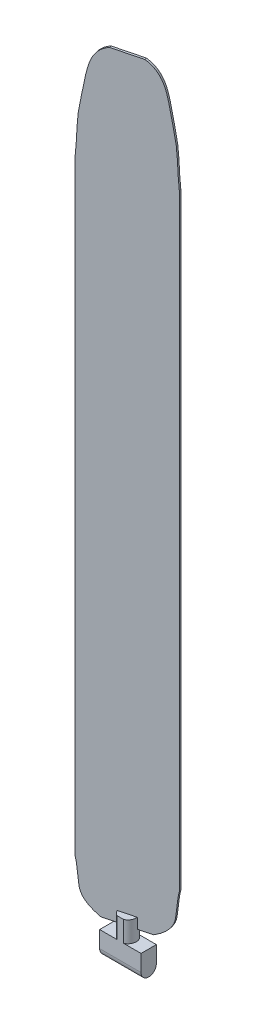
SolidWorks part; units mm, degrees
ref_plane "前视基准面" through (0, 0, 0) normal (0, 0, 1) x (1, 0, 0)
ref_plane "上视基准面" through (0, 0, 0) normal (0, 1, 0) x (1, 0, 0)
ref_plane "右视基准面" through (0, 0, 0) normal (1, 0, 0) x (0, 0, -1)
sketch "草图2" plane through (-29.3521, 0, 0) normal (1, 0, 0) x (0, 0, -1)
  line L1 (-34.5848, 63.5175) -> (-34.5848, 71.5175)
  line L2 (-34.5848, 71.5175) -> (-27.1848, 71.5175)
  line L3 (-27.1848, 71.5175) -> (-27.1848, 63.5175)
  arc A0 (-34.5848, 63.5175) -> (-27.1848, 63.5175) centre (-30.8848, 63.5175) ccw
  dimension "D1" = 8
extrude "凸台-拉伸1" add sketch "草图2" along normal mid plane 20
sketch "草图3" plane through (-29.3521, 0, 0) normal (1, 0, 0) x (0, 0, -1)
  line L0 (-34.5848, 67.3112) -> (-34.5848, -30.2762)
  line L1 (-34.5848, 18.5175) -> (-2.454, 18.5175)
sketch "草图4" plane through (0, 71.5175, 0) normal (0, 1, 0) x (1, 0, 0)
  line L0 (-39.3521, -34.5848) -> (-19.3521, -27.1848)
  line L4 (-39.3521, -27.1848) -> (-39.3521, -34.5848)
  line L5 (-39.3521, -34.5848) -> (-19.3521, -34.5848)
  line L6 (-19.3521, -34.5848) -> (-19.3521, -27.1848)
  line L7 (-19.3521, -27.1848) -> (-39.3521, -27.1848)
  line L8 (-39.3521, -27.1848) -> (-39.3521, -34.5848)
  line L9 (-39.3521, -34.5848) -> (-19.3521, -34.5848)
  line L10 (-19.3521, -34.5848) -> (-19.3521, -27.1848)
  line L11 (-19.3521, -27.1848) -> (-39.3521, -27.1848)
  circle A0 centre (-29.3521, -30.8848) radius 4
  dimension "D2" = 8
  dimension "D1" = 0
extrude "凸台-拉伸2" add sketch "草图4" along normal blind 10 contours L9 A0 L0 | L0 A0 L11
sketch "草图7" plane through (0, 81.5175, 0) normal (0, 1, 0) x (1, 0, 0)
  line L0 (-49.2279, -36.4994) -> (-49.4764, -35.5308)
  line L1 (-49.4764, -35.5308) -> (-9.4764, -25.2702)
  line L2 (-9.4764, -25.2702) -> (-9.2279, -26.2388)
  line L3 (-9.2279, -26.2388) -> (-49.2279, -36.4994)
extrude "凸台-拉伸3" add sketch "草图7" along normal blind 360 and the other way blind 5
sketch "草图8" plane through (5.7454, 0, 22.3979) normal (0.2485, 0, 0.9686) x (0.9686, 0, -0.2485)
  line L0 (-56.7531, 76.5175) -> (-40.0742, 76.5175) construction
  line L1 (-56.7531, 76.5175) -> (-56.7531, 441.5175) construction
  line L2 (-56.7531, 441.5175) -> (-15.4581, 441.5175) construction
  line L3 (-36.1056, 441.5175) -> (-36.1056, 74.8978)
  line L4 (-46.6104, 76.5175) -> (-56.7531, 76.5175)
  line L5 (-56.7531, 76.5175) -> (-56.7531, 98.1797)
  line L6 (-15.4581, 98.1797) -> (-9.3936, 70.7026)
  line L7 (-9.3936, 70.7026) -> (-25.6008, 76.5175)
  line L8 (-43.0788, 441.5175) -> (-63.9555, 450.3371)
  line L9 (-63.9555, 450.3371) -> (-56.7531, 391.6929)
  line L10 (-29.1324, 441.5175) -> (-6.3029, 450.3371)
  line L11 (-6.3029, 450.3371) -> (-15.4581, 391.6929)
  spline S0 degree 3 poles (-46.6104, 76.5175) (-49.5539, 78.056) (-54.6034, 81.6398) (-56.8541, 96.7002) (-55.5007, 110.1189) (-76.2804, 100.3016) knots 0 0 0 0 0.237372 0.354243 1 1 1 1
  spline S1 degree 3 poles (-43.0788, 441.5175) (-51.2168, 438.2306) (-52.5763, 425.1129) (-57.3359, 403.6983) (-55.3283, 388.6097) (-60.2338, 378.7441) knots 0 0 0 0 0.351967 0.523137 1 1 1 1
  spline S2 degree 3 poles (-29.1324, 441.5175) (-20.9944, 438.2306) (-19.6349, 425.1129) (-14.8753, 403.6983) (-16.8829, 388.6097) (-11.9774, 378.7441) knots 0 0 0 0 0.351967 0.523137 1 1 1 1
  spline S3 degree 3 poles (-25.6008, 76.5175) (-22.6573, 78.056) (-17.6078, 81.6398) (-15.3571, 96.7002) (-16.7105, 110.1189) (4.0692, 100.3016) knots 0 0 0 0 0.237372 0.354243 1 1 1 1
  line M2 (-32.137, 76.5175) -> (-15.4581, 76.5175)
  line M3 (-15.4581, 76.5175) -> (-15.4581, 441.5175)
  line M4 (-15.4581, 441.5175) -> (-56.7531, 441.5175)
  line M5 (-56.7531, 441.5175) -> (-56.7531, 76.5175)
  line M6 (-56.7531, 76.5175) -> (-40.0742, 76.5175)
extrude "切除-拉伸1" cut sketch "草图8" against normal through all and the other way through all contours S1 M4 M5 | S2 M4 M3 | S3 M2 M3 | S0 M6 M5
